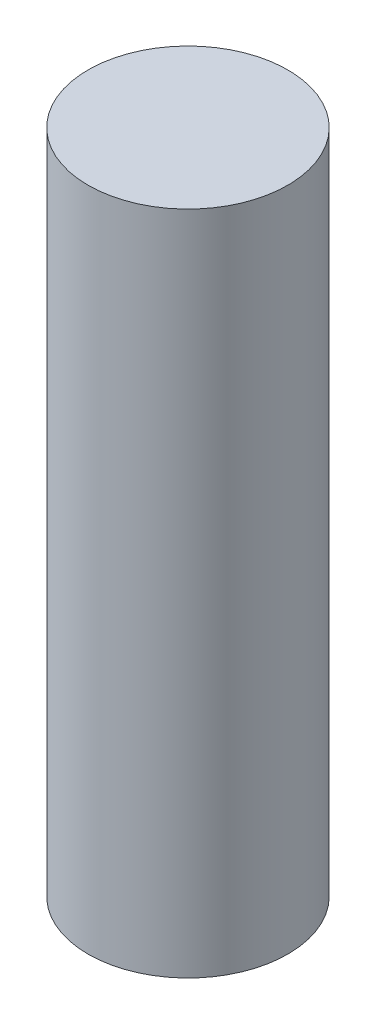
SolidWorks part; units mm, degrees
ref_plane "Front" through (0, 0, 0) normal (0, 0, 1) x (1, 0, 0)
ref_plane "Top" through (0, 0, 0) normal (0, 1, 0) x (1, 0, 0)
ref_plane "Right" through (0, 0, 0) normal (1, 0, 0) x (0, 0, -1)
sketch "Sketch1" plane through (0, 0, 0) normal (0, 1, 0) x (1, 0, 0)
  circle A0 centre (0, 0) radius 7.5
  dimension "D1" = 15
extrude "Boss-Extrude1" add sketch "Sketch1" along normal blind 50
